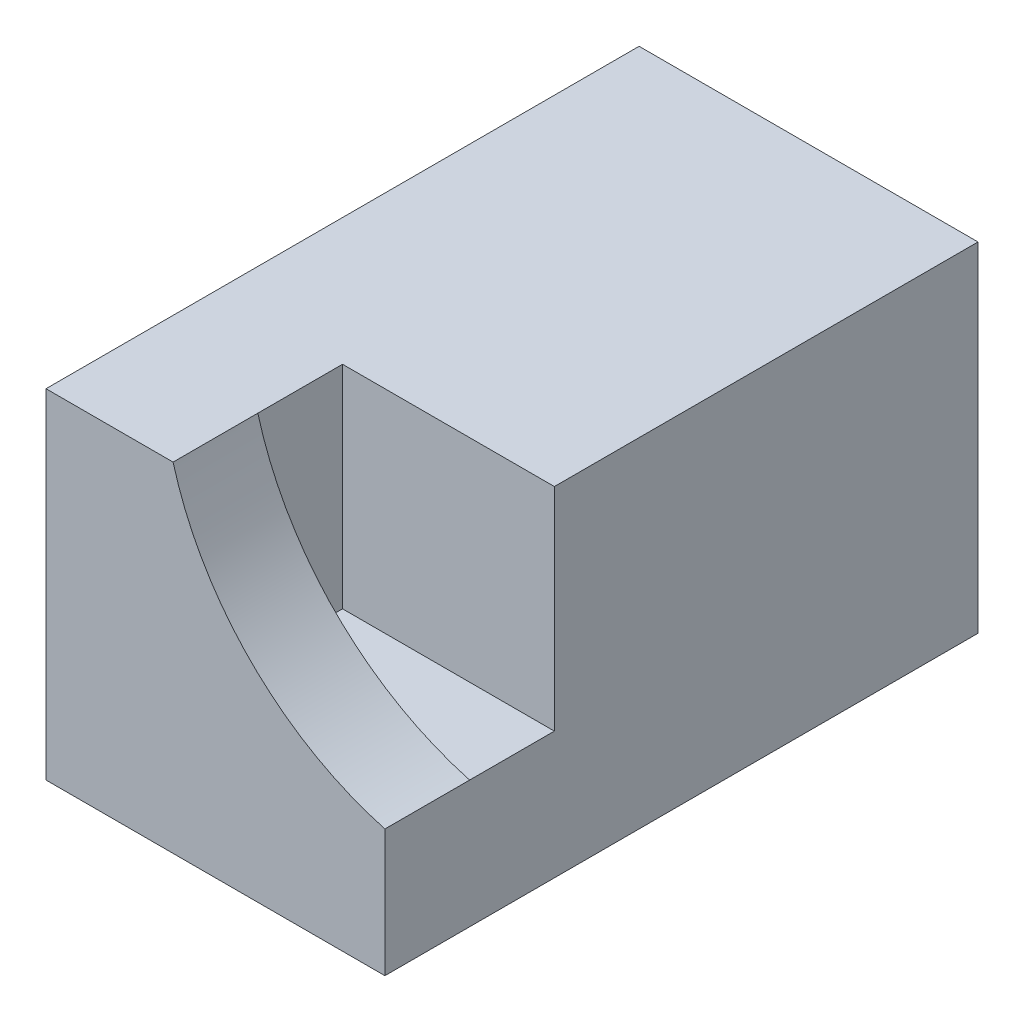
SolidWorks part; units mm, degrees
ref_plane "Płaszczyzna przednia" through (0, 0, 0) normal (0, 0, 1) x (1, 0, 0)
ref_plane "Płaszczyzna górna" through (0, 0, 0) normal (0, 1, 0) x (1, 0, 0)
ref_plane "Płaszczyzna prawa" through (0, 0, 0) normal (1, 0, 0) x (0, 0, -1)
sketch "Szkic1" plane through (0, 0, 0) normal (0, 0, 1) x (1, 0, 0)
  line L1 (0, 0) -> (8, 0)
  line L2 (0, 0) -> (0, 8)
  line L3 (0, 8) -> (8, 8)
  line L4 (8, 0) -> (8, 8)
  dimension "D1" = 8
  dimension "D2" = 8
extrude "Dodanie-wyciągnięcie1" add sketch "Szkic1" along normal blind 14
sketch "Szkic3" plane through (0, 0, 0) normal (0, 0, -1) x (-1, 0, 0)
  line L0 (0, 0) -> (-8, 0) construction
  line L1 (-8, 0) -> (-8, 8) construction
  circle A0 centre (-4, 4) radius 1.375
  dimension "D3" = 2.75
  dimension "D1" = 4
  dimension "D2" = 4
extrude "Wytnij-wyciągnięcie1" cut sketch "Szkic3" against normal blind 8
sketch "Szkic6" plane through (0, 0, 14) normal (0, 0, 1) x (1, 0, 0)
  line L0 (8, 8) -> (0, 8) construction
  line L1 (3, 8) -> (8, 8)
  line L2 (3, 8) -> (3, 3)
  line L3 (3, 3) -> (8, 3)
  line L4 (8, 8) -> (8, 3)
  line L5 (8, 0) -> (8, 8) construction
  line L6 (0, 8) -> (0, 0) construction
  line L7 (0, 0) -> (8, 0) construction
  circle A0 centre (9.8978, 9.8978) radius 7.1541
  line M5 (8, 0) -> (8, 8)
  line M6 (8, 8) -> (0, 8)
  dimension "D1" = 3
  dimension "D2" = 3
extrude "Wytnij-wyciągnięcie4" cut sketch "Szkic6" against normal blind 4 contours A0 M6 M5
sketch "Szkic7" plane through (0, 8, 0) normal (0, 1, 0) x (1, 0, 0)
  line L0 (8, -10) -> (8, -14) construction
  line L1 (3, -10) -> (8, -10)
  line L2 (3, -10) -> (3, -12)
  line L3 (3, -12) -> (8, -12)
  line L4 (8, -10) -> (8, -12)
  dimension "D1" = 2
extrude "Wytnij-wyciągnięcie5" cut sketch "Szkic7" against normal blind 5
